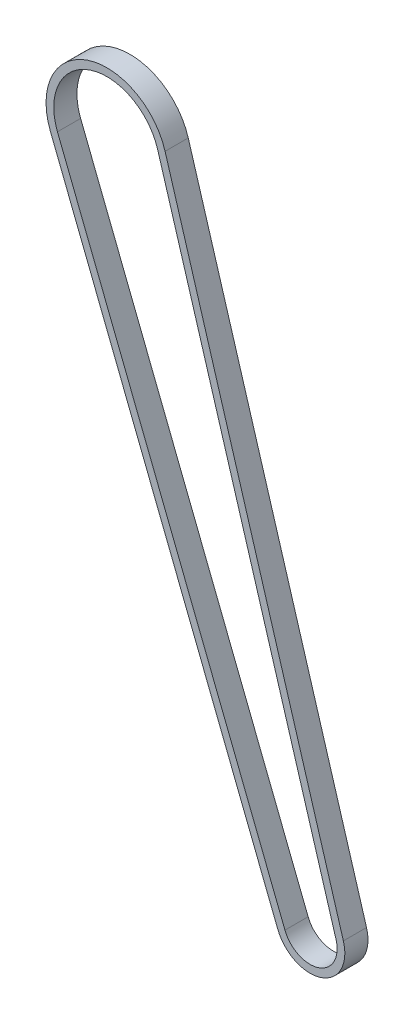
SolidWorks part; units mm, degrees
ref_plane "Plan de face" through (0, 0, 0) normal (0, 0, 1) x (1, 0, 0)
ref_plane "Plan de dessus" through (0, 0, 0) normal (0, 1, 0) x (1, 0, 0)
ref_plane "Plan de droite" through (0, 0, 0) normal (1, 0, 0) x (0, 0, -1)
sketch "Esquisse2" plane through (0, 0, 0) normal (0, 0, 1) x (1, 0, 0)
  line L0 (0, 0) -> (1, 0) construction
  line L1 (0, 0) -> (0, 1) construction
  line L2 (-8.3739, -3.298) -> (-67.3132, 146.3535)
  line L3 (-37.5723, 156.6484) -> (8.6208, 2.5848)
  arc A0 (8.6208, 2.5848) -> (-8.3739, -3.298) centre (0, 0) cw
  arc A1 (-67.3132, 146.3535) -> (-37.5723, 156.6484) centre (-52.6588, 152.125) cw
extrude "Extru.-Mince1" add sketch "Esquisse2" against normal blind 6 from vertex thin
